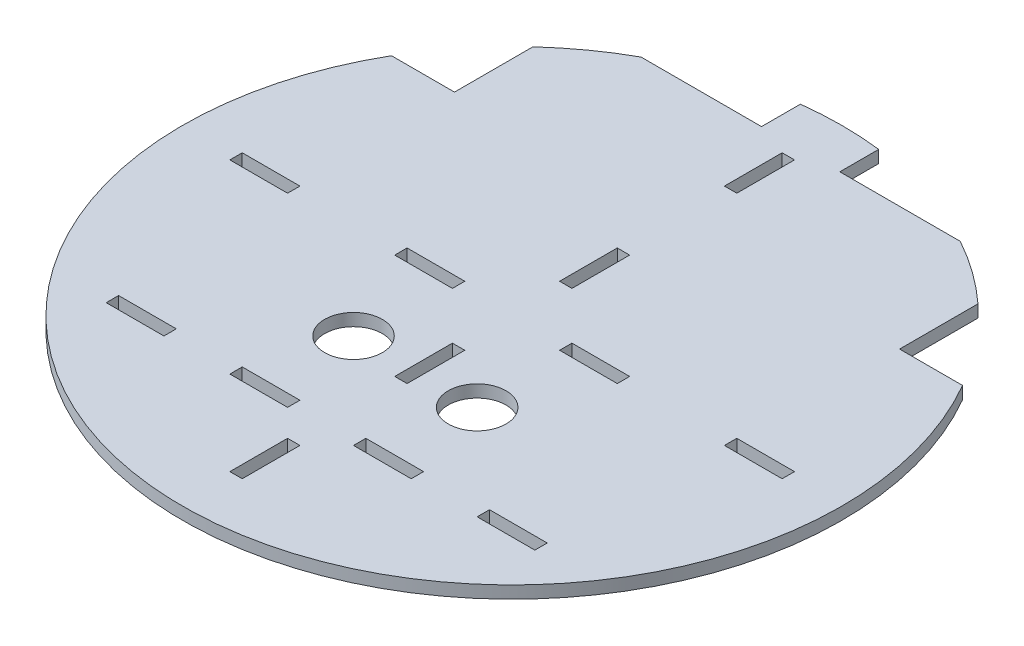
SolidWorks part; units mm, degrees
ref_plane "Front Plane" through (0, 0, 0) normal (0, 0, 1) x (1, 0, 0)
ref_plane "Top Plane" through (0, 0, 0) normal (0, 1, 0) x (1, 0, 0)
ref_plane "Right Plane" through (0, 0, 0) normal (1, 0, 0) x (0, 0, -1)
sketch "Sketch1" plane through (0, 0, 0) normal (0, 1, 0) x (1, 0, 0)
  circle A0 centre (0, 0) radius 80
  dimension "D1" = 160
extrude "Boss-Extrude1" add sketch "Sketch1" along normal blind 3 contours A0
sketch "Sketch2" plane through (0, 3, 0) normal (0, 1, 0) x (1, 0, 0)
  line L0 (-1.5, 27) -> (1.5, 27)
  line L1 (-1.5, 27) -> (-1.5, 13)
  line L2 (-1.5, 13) -> (1.5, 13)
  line L3 (1.5, 27) -> (1.5, 13)
  line L4 (-1.5, 27) -> (1.5, 13) construction
  line L5 (-1.5, 13) -> (1.5, 27) construction
  line L6 (-1.5, 67) -> (1.5, 67)
  line L7 (-1.5, 67) -> (-1.5, 53)
  line L8 (-1.5, 53) -> (1.5, 53)
  line L9 (1.5, 67) -> (1.5, 53)
  line L10 (-1.5, 67) -> (1.5, 53) construction
  line L11 (-1.5, 53) -> (1.5, 67) construction
  line L12 (-27, 1.5) -> (-13, 1.5)
  line L13 (-27, 1.5) -> (-27, -1.5)
  line L14 (-27, -1.5) -> (-13, -1.5)
  line L15 (-13, 1.5) -> (-13, -1.5)
  line L16 (-27, 1.5) -> (-13, -1.5) construction
  line L17 (-27, -1.5) -> (-13, 1.5) construction
  line L18 (-67, 1.5) -> (-53, 1.5)
  line L19 (-67, 1.5) -> (-67, -1.5)
  line L20 (-67, -1.5) -> (-53, -1.5)
  line L21 (-53, 1.5) -> (-53, -1.5)
  line L22 (-67, 1.5) -> (-53, -1.5) construction
  line L23 (-67, -1.5) -> (-53, 1.5) construction
  line L24 (13, 1.5) -> (27, 1.5)
  line L25 (13, 1.5) -> (13, -1.5)
  line L26 (13, -1.5) -> (27, -1.5)
  line L27 (27, 1.5) -> (27, -1.5)
  line L28 (13, 1.5) -> (27, -1.5) construction
  line L29 (13, -1.5) -> (27, 1.5) construction
  line L30 (53, 1.5) -> (67, 1.5)
  line L31 (53, 1.5) -> (53, -1.5)
  line L32 (53, -1.5) -> (67, -1.5)
  line L33 (67, 1.5) -> (67, -1.5)
  line L34 (53, 1.5) -> (67, -1.5) construction
  line L35 (53, -1.5) -> (67, 1.5) construction
  line L36 (-1.5, -13) -> (1.5, -13)
  line L37 (-1.5, -13) -> (-1.5, -27)
  line L38 (-1.5, -27) -> (1.5, -27)
  line L39 (1.5, -13) -> (1.5, -27)
  line L40 (-1.5, -13) -> (1.5, -27) construction
  line L41 (-1.5, -27) -> (1.5, -13) construction
  line L42 (-1.5, -53) -> (1.5, -53)
  line L43 (-1.5, -53) -> (-1.5, -67)
  line L44 (-1.5, -67) -> (1.5, -67)
  line L45 (1.5, -53) -> (1.5, -67)
  line L46 (-1.5, -53) -> (1.5, -67) construction
  line L47 (-1.5, -67) -> (1.5, -53) construction
  line L48 (-22, -43.5) -> (-8, -43.5)
  line L49 (-22, -43.5) -> (-22, -46.5)
  line L50 (-22, -46.5) -> (-8, -46.5)
  line L51 (-8, -43.5) -> (-8, -46.5)
  line L52 (-22, -43.5) -> (-8, -46.5) construction
  line L53 (-22, -46.5) -> (-8, -43.5) construction
  line L54 (8, -43.5) -> (22, -43.5)
  line L55 (8, -43.5) -> (8, -46.5)
  line L56 (8, -46.5) -> (22, -46.5)
  line L57 (22, -43.5) -> (22, -46.5)
  line L58 (8, -43.5) -> (22, -46.5) construction
  line L59 (8, -46.5) -> (22, -43.5) construction
  line L60 (-52, -43.5) -> (-38, -43.5)
  line L61 (-52, -43.5) -> (-52, -46.5)
  line L62 (-52, -46.5) -> (-38, -46.5)
  line L63 (-38, -43.5) -> (-38, -46.5)
  line L64 (-52, -43.5) -> (-38, -46.5) construction
  line L65 (-52, -46.5) -> (-38, -43.5) construction
  line L66 (38, -43.5) -> (52, -43.5)
  line L67 (38, -43.5) -> (38, -46.5)
  line L68 (38, -46.5) -> (52, -46.5)
  line L69 (52, -43.5) -> (52, -46.5)
  line L70 (38, -43.5) -> (52, -46.5) construction
  line L71 (38, -46.5) -> (52, -43.5) construction
  point P0 (-27, 0)
  point P1 (0, 20)
  point P6 (20, 0)
  point P7 (0, 60)
  point P12 (-20, 0)
  point P18 (-60, 0)
  point P26 (0, -20)
  point P27 (60, 0)
  point P36 (0, -60)
  point P41 (-15, -45)
  point P46 (45, -45)
  point P47 (-45, -45)
  point P49 (15, -45)
  dimension "D1" = 14
  dimension "D2" = 14
  dimension "D3" = 3
  dimension "D4" = 3
  dimension "D5" = 14
  dimension "D6" = 3
  dimension "D7" = 14
  dimension "D8" = 3
  dimension "D9" = 14
  dimension "D10" = 3
  dimension "D11" = 3
  dimension "D12" = 14
  dimension "D13" = 14
  dimension "D14" = 3
  dimension "D15" = 16
  dimension "D16" = 3
  dimension "D17" = 14
  dimension "D18" = 3
  dimension "D19" = 14
  dimension "D20" = 3
  dimension "D21" = 14
  dimension "D22" = 3
  dimension "D23" = 3
  dimension "D24" = 14
  dimension "D25" = 26
  dimension "D26" = 26
  dimension "D27" = 26
  dimension "D28" = 26
  dimension "D29" = 26
  dimension "D30" = 16
  dimension "D31" = 14
  dimension "D32" = 16
  dimension "D33" = 6.5
  dimension "D34" = 16.5
  dimension "D35" = 13
  dimension "D36" = 13
  dimension "D37" = 13
  dimension "D38" = 1.5
  dimension "D39" = 1.5
extrude "Cut-Extrude1" cut sketch "Sketch2" against normal blind 3
sketch "Sketch3" plane through (0, 3, 0) normal (0, 1, 0) x (1, 0, 0)
  line L0 (-69.282, 40) -> (-54, 40)
  line L1 (-54, 40) -> (-54, 59.0254)
  circle A0 centre (0, 0) radius 80 construction
  dimension "D1" = 19.0254
  dimension "D2" = 15.282
extrude "Cut-Extrude3" cut sketch "Sketch3" against normal blind 3 and the other way through all
sketch "Sketch4" plane through (0, 3, 0) normal (0, 1, 0) x (1, 0, 0)
  line L0 (69.282, 40) -> (54, 40)
  line L1 (54, 40) -> (54, 59.0254)
  arc A0 (-69.282, 40) -> (-54, 59.0254) centre (0, 0) ccw construction
  dimension "D1" = 19.0254
  dimension "D2" = 15.282
extrude "Cut-Extrude4" cut sketch "Sketch4" against normal blind 3 and the other way through all flip side to cut
sketch "Sketch5" plane through (0, 3, 0) normal (0, 1, 0) x (1, 0, 0)
  line L0 (-38.7298, 70) -> (-9.5, 70)
  line L1 (-9.5, 79.4339) -> (-9.5, 70)
  arc A0 (54, 59.0254) -> (-54, 59.0254) centre (0, 0) ccw construction
  dimension "D1" = 29.2298
  dimension "D2" = 9.4339
extrude "Cut-Extrude5" cut sketch "Sketch5" against normal blind 3 and the other way through all flip side to cut
sketch "Sketch6" plane through (0, 3, 0) normal (0, 1, 0) x (1, 0, 0)
  line L0 (38.7298, 70) -> (9.5, 70)
  line L1 (9.5, 70) -> (9.5, 79.4339)
  arc A0 (54, 59.0254) -> (-9.5, 79.4339) centre (0, 0) ccw construction
  dimension "D1" = 29.2298
  dimension "D2" = 9.4339
extrude "Cut-Extrude6" cut sketch "Sketch6" against normal blind 3 and the other way through all flip side to cut
sketch "Sketch7" plane through (0, 3, 0) normal (0, 1, 0) x (1, 0, 0)
  line L0 (0, -80) -> (0, 0) construction
  arc A0 (-69.282, 40) -> (69.282, 40) centre (0, 0) ccw construction
  circle A1 centre (-15, -23.5) radius 7
  circle A2 centre (15, -23.5) radius 7
extrude "Cut-Extrude7" cut sketch "Sketch7" against normal blind 3
sketch "Sketch8" plane through (0, 3, 0) normal (0, 1, 0) x (1, 0, 0)
  text T0 "HX3" font "Century Gothic" height in points 20
  dimension "D1" = 7.1834
  dimension "D2" = 2.2987
